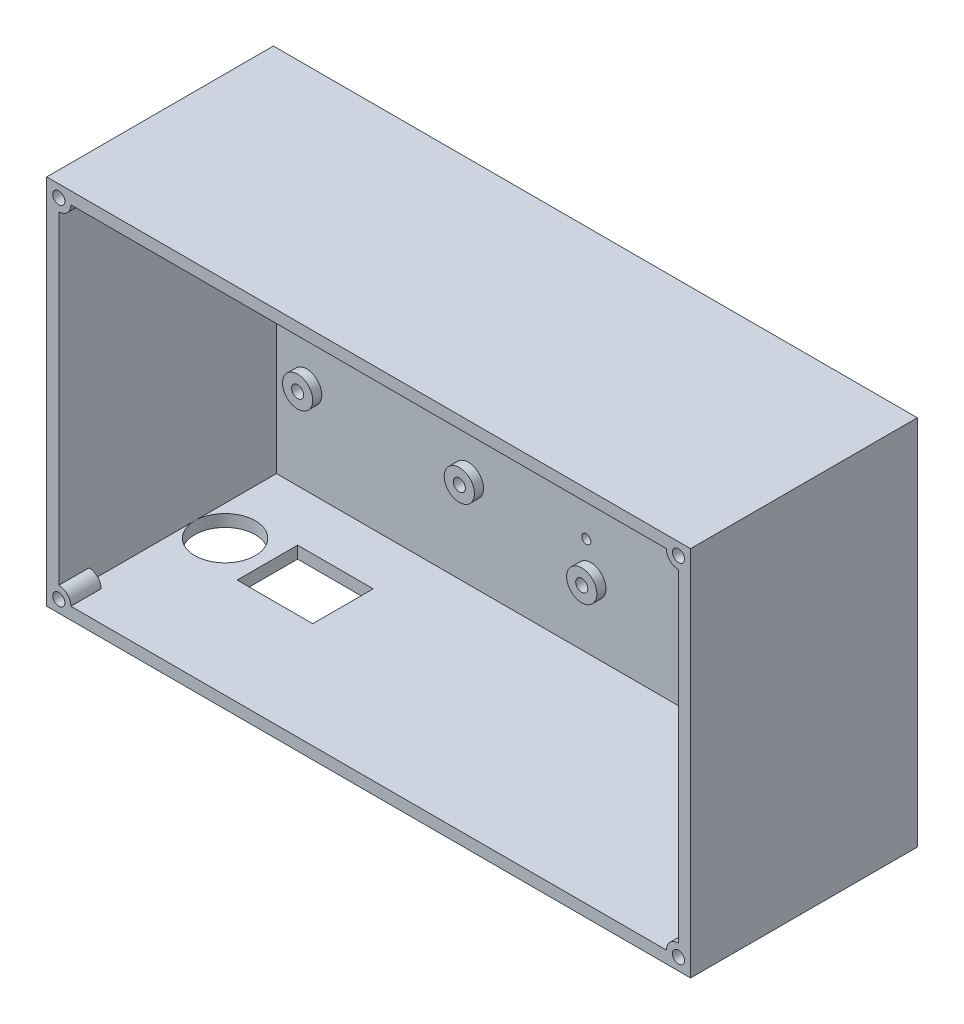
SolidWorks part; units mm, degrees
ref_plane "Front Plane" through (0, 0, 0) normal (0, 0, 1) x (1, 0, 0)
ref_plane "Top Plane" through (0, 0, 0) normal (0, 1, 0) x (1, 0, 0)
ref_plane "Right Plane" through (0, 0, 0) normal (1, 0, 0) x (0, 0, -1)
sketch "Sketch1" plane through (0, 0, 0) normal (0, 0, 1) x (1, 0, 0)
  line L1 (-102.5, -57.5) -> (102.5, -57.5)
  line L2 (-102.5, -57.5) -> (-102.5, 57.5)
  line L3 (-102.5, 57.5) -> (102.5, 57.5)
  line L4 (102.5, -57.5) -> (102.5, 57.5)
  line L5 (-102.5, -57.5) -> (102.5, 57.5) construction
  line L6 (-102.5, 57.5) -> (102.5, -57.5) construction
  point P0 (0, 0)
  dimension "D1" = 205
  dimension "D2" = 115
extrude "Boss-Extrude1" add sketch "Sketch1" along normal blind 3
sketch "Sketch2" plane through (0, 0, 3) normal (0, 0, 1) x (1, 0, 0)
  line L0 (-102.5, 57.5) -> (-102.5, -57.5) construction
  line L1 (102.5, 57.5) -> (-102.5, 57.5) construction
  circle A0 centre (-92.5, 32.5) radius 2
  circle A1 centre (-92.5, 32.5) radius 5
  circle A2 centre (-92.5, -27.5) radius 2
  circle A3 centre (-92.5, -27.5) radius 5
  circle A4 centre (-39, 32.5) radius 2
  circle A5 centre (-39, 32.5) radius 5
  circle A6 centre (-39, -27.5) radius 2
  circle A7 centre (-39, -27.5) radius 5
  point P16 (0, 0)
  dimension "D1" = 4
  dimension "D2" = 10
  dimension "D5" = 4
  dimension "D6" = 10
  dimension "D7" = 4
  dimension "D8" = 10
  dimension "D9" = 4
  dimension "D10" = 10
  dimension "D3" = 10
  dimension "D4" = 25
  dimension "D11" = 60
  dimension "D12" = 60
  dimension "D13" = 0
  dimension "D14" = 53.5
  dimension "D15" = 53.5
  dimension "D16" = 10
extrude "Boss-Extrude2" add sketch "Sketch2" along normal blind 3
sketch "Sketch3" plane through (0, 0, 3) normal (0, 0, 1) x (1, 0, 0)
  line L0 (102.5, 57.5) -> (-102.5, 57.5) construction
  line L1 (102.5, -57.5) -> (102.5, 57.5) construction
  circle A0 centre (1.5, 40) radius 2
  circle A1 centre (1.5, 40) radius 5
  circle A2 centre (82.5, -36) radius 2
  circle A3 centre (82.5, -36) radius 5
  circle A4 centre (82.5, 40) radius 2
  circle A5 centre (82.5, 40) radius 5
  circle A6 centre (1.5, -36) radius 2
  circle A7 centre (1.5, -36) radius 5
  point P12 (33.6413, 9.0966)
  point P13 (53.7684, 28.0612)
  point P14 (54.787, 7.7801)
  dimension "D1" = 4
  dimension "D2" = 10
  dimension "D3" = 81
  dimension "D4" = 76
  dimension "D5" = 0
  dimension "D6" = 17.5
  dimension "D7" = 76
  dimension "D8" = 20
  dimension "D9" = 81
  dimension "D10" = 0
extrude "Boss-Extrude3" add sketch "Sketch3" along normal blind 3
sketch "Sketch5" plane through (0, 0, 0) normal (0, 0, -1) x (-1, 0, 0)
  line L0 (-106.5, 61.5) -> (-106.5, -61.5)
  line L1 (-106.5, -61.5) -> (106.5, -61.5)
  line L2 (106.5, -61.5) -> (106.5, 61.5)
  line L3 (106.5, 61.5) -> (-106.5, 61.5)
  line L4 (-102.5, 57.5) -> (-102.5, -57.5)
  line L5 (-102.5, -57.5) -> (102.5, -57.5)
  line L6 (102.5, -57.5) -> (102.5, 57.5)
  line L7 (102.5, 57.5) -> (-102.5, 57.5)
  line L8 (-102.5, 57.5) -> (-102.5, -57.5)
  line L9 (-102.5, -57.5) -> (102.5, -57.5)
  line L10 (102.5, -57.5) -> (102.5, 57.5)
  line L11 (102.5, 57.5) -> (-102.5, 57.5)
  dimension "D1" = 0
  dimension "D2" = 4
extrude "Boss-Extrude4" add sketch "Sketch5" against normal blind 75
hole_wizard "Ø3.0mm Clearance Dowel Hole1" positions "Sketch7" profile "Sketch8" hole size "Ø3.0" standard "ISO"
sketch "Sketch7" plane through (0, 0, 3) normal (0, 0, 1) x (1, 0, 0)
  point P0 (0, 25)
  point P2 (0, -25)
  dimension "D1" = 50
  dimension "D2" = 25
sketch "Sketch8" plane through (0, 25, 3) normal (1, 0, 0) x (0, -1, 0)
  line L0 (0, 0) -> (0, 30.9013)
  line L1 (0, 30.9013) -> (1.5, 30)
  line L2 (1.5, 30) -> (1.5, 0)
  line L5 (1.5, 0) -> (0, 0)
  line L10 (0, 30.9013) -> (-1.5, 30) construction
  line L11 (0, -6.35) -> (0, 107.95) construction
  dimension "Hole Dia." = 3
  dimension "Hole Depth" = 30
  dimension "Drill Angle" = 118
sketch "Sketch10" plane through (0, -61.5, 0) normal (0, -1, 0) x (1, 0, 0)
  line L0 (-78.5, 20) -> (-78.5, 40)
  line L1 (-106.5, 75) -> (-106.5, 0) construction
  line L2 (-78.5, 20) -> (-53.5, 20)
  line L3 (106.5, 0) -> (-106.5, 0) construction
  line L4 (-78.5, 40) -> (-53.5, 40)
  line L5 (-53.5, 40) -> (-53.5, 20)
  dimension "D1" = 20
  dimension "D2" = 28
  dimension "D3" = 25
  dimension "D4" = 20
extrude "Cut-Extrude1" cut sketch "Sketch10" against normal blind 4
sketch "Sketch11" plane through (0, -61.5, 0) normal (0, -1, 0) x (1, 0, 0)
  line L0 (-106.5, 75) -> (-106.5, 0) construction
  circle A0 centre (-92.5, 30) radius 10
  point P2 (-92.3014, 30)
  dimension "D1" = 20
  dimension "D2" = 14
extrude "Cut-Extrude2" cut sketch "Sketch11" against normal blind 4
sketch "Sketch12" plane through (0, 0, 75) normal (0, 0, 1) x (1, 0, 0)
  circle A0 centre (102.5, -57.5) radius 2
  circle A1 centre (102.5, -57.5) radius 4
  circle A2 centre (102.5, 57.5) radius 4
  circle A3 centre (-102.5, 57.5) radius 4
  circle A4 centre (-102.5, -57.5) radius 4
extrude "Boss-Extrude5" add sketch "Sketch12" against normal blind 10
sketch "Sketch13" plane through (0, 0, 75) normal (0, 0, 1) x (1, 0, 0)
  circle A0 centre (102.5, -57.5) radius 2
  circle A1 centre (102.5, 57.5) radius 2
  circle A2 centre (-102.5, 57.5) radius 2
  circle A3 centre (-102.5, -57.5) radius 2
extrude "Cut-Extrude3" cut sketch "Sketch13" against normal blind 10
